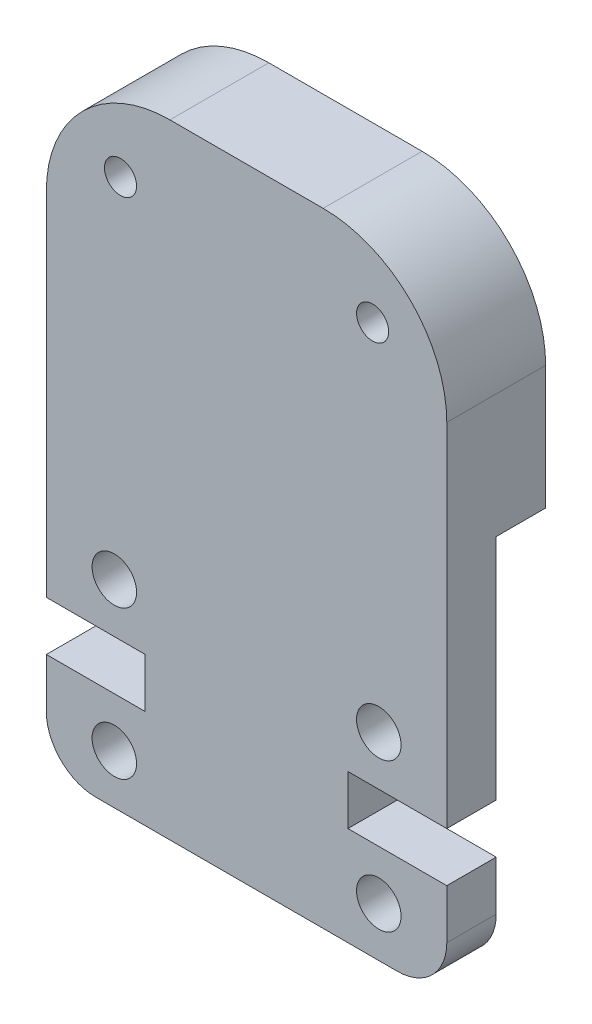
SolidWorks part; units mm, degrees
ref_plane "Front Plane" through (0, 0, 0) normal (0, 0, 1) x (1, 0, 0)
ref_plane "Top Plane" through (0, 0, 0) normal (0, 1, 0) x (1, 0, 0)
ref_plane "Right Plane" through (0, 0, 0) normal (1, 0, 0) x (0, 0, -1)
sketch "Sketch1" plane through (0, 0, 0) normal (0, 0, 1) x (1, 0, 0)
  line L0 (8.1, 25.23) -> (8.1, 0) construction
  line L1 (2, 0) -> (14.2, 0)
  line L2 (5, 25.23) -> (11.2, 25.23)
  line L3 (12.2, 4) -> (16.2, 4)
  line L4 (12.2, 6) -> (12.2, 4)
  line L5 (16.2, 6) -> (12.2, 6)
  line L6 (16.2, 2) -> (16.2, 4)
  line L7 (16.2, 20.23) -> (16.2, 6)
  line L22 (0, 20.23) -> (0, 6)
  line L33 (0, 2) -> (0, 4)
  line L34 (0, 6) -> (4, 6)
  line L36 (4, 6) -> (4, 4)
  line L37 (4, 4) -> (0, 4)
  circle A0 centre (13.45, 2) radius 0.9
  arc A1 (16.2, 2) -> (14.2, 0) centre (14.2, 2) cw
  circle A2 centre (13.2, 22.23) radius 0.65
  arc A3 (11.2, 25.23) -> (16.2, 20.23) centre (11.2, 20.23) cw
  circle A4 centre (2.75, 8) radius 0.9
  circle A5 centre (13.45, 8) radius 0.9
  arc A17 (5, 25.23) -> (0, 20.23) centre (5, 20.23) ccw
  circle A19 centre (3, 22.23) radius 0.65
  arc A21 (0, 2) -> (2, 0) centre (2, 2) ccw
  circle A23 centre (2.75, 2) radius 0.9
  dimension "D1" = 1.3
  dimension "D2" = 6
  dimension "D3" = 5
  dimension "D4" = 2
  dimension "D14" = 1.8
  dimension "D10" = 1.8
  dimension "D11" = 1.8
  dimension "D15" = 1.8
  dimension "D5" = 3
  dimension "D6" = 2.75
  dimension "D7" = 8.1
  dimension "D8" = 2.75
  dimension "D9" = 4
  dimension "D12" = 3
  dimension "D13" = 25.23
extrude "Boss-Extrude1" add sketch "Sketch1" along normal blind 4
sketch "Sketch2" plane through (0, 0, 0) normal (0, 0, 1) x (1, 0, 0)
  line L0 (0, 0) -> (16.2, 0)
  line L1 (16.2, 0) -> (16.2, 15.23)
  line L2 (16.2, 15.23) -> (0, 15.23)
  line L3 (0, 15.23) -> (0, 0)
  dimension "D1" = 15.23
extrude "Cut-Extrude1" cut sketch "Sketch2" along normal blind 2
equation "\"D7@Sketch1\"= \"fingerWidth@parametersSketch@prostheticParameters.SLDPRT\" / 2 'DIP width"
equation "\"D13@Sketch1\"= \"HL@parametersSketch@prostheticParameters.SLDPRT\" * 0.158 - 4 'DIP length - Sil. Sht DIP"
equation "\"D1@Sketch2\"= \"HL@parametersSketch@prostheticParameters.SLDPRT\" * 0.158 - 4 - 10 'DIP Cut fingertip"
equation "\"D1@Sketch1\"= 1 + \"tol1@parametersSketch@prostheticParameters.SLDPRT\""
equation "\"D10@Sketch1\"= 1.5 + \"tol1@parametersSketch@prostheticParameters.SLDPRT\""
equation "\"D11@Sketch1\"= 1.5 + \"tol1@parametersSketch@prostheticParameters.SLDPRT\""
equation "\"D14@Sketch1\"= 1.5 + \"tol1@parametersSketch@prostheticParameters.SLDPRT\""
equation "\"D15@Sketch1\"= 1.5 + \"tol1@parametersSketch@prostheticParameters.SLDPRT\""
